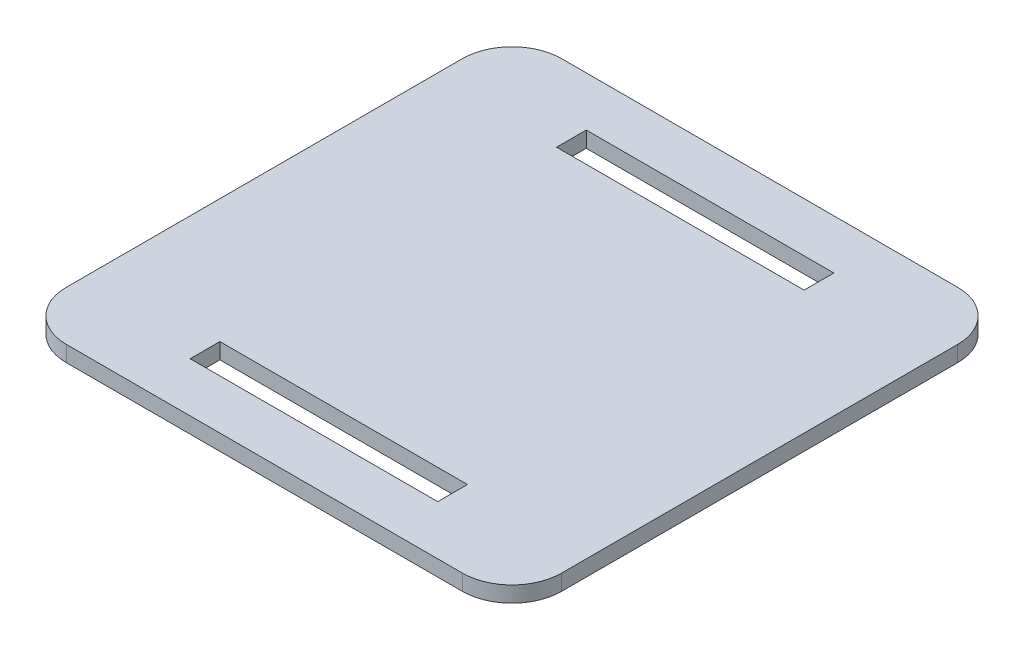
SolidWorks part; units mm, degrees
ref_plane "Front Plane" through (0, 0, 0) normal (0, 0, 1) x (1, 0, 0)
ref_plane "Top Plane" through (0, 0, 0) normal (0, 1, 0) x (1, 0, 0)
ref_plane "Right Plane" through (0, 0, 0) normal (1, 0, 0) x (0, 0, -1)
sketch "Sketch1" plane through (0, 0, 0) normal (0, 1, 0) x (1, 0, 0)
  line L0 (0, 0) -> (0, 50)
  line L1 (0, 0) -> (50, 0)
  line L2 (0, 50) -> (50, 50)
  line L3 (50, 0) -> (50, 50)
  point P0 (0, 0)
extrude "Boss-Extrude1" add sketch "Sketch1" along normal blind 1.6
sketch "Sketch2" plane through (0, 0, 0) normal (0, -1, 0) x (1, 0, 0)
  line L3 (12.5, -5) -> (12.5, -8)
  line L4 (12.5, -5) -> (37.5, -5)
  line L5 (12.5, -8) -> (12.5, -5)
  line L6 (12.5, -8) -> (37.5, -8)
  line L7 (12.5, -5) -> (37.5, -5)
  line L8 (37.5, -8) -> (37.5, -5)
  line L10 (12.5, -45) -> (37.5, -45)
  line L11 (12.5, -45) -> (12.5, -42)
  line L12 (37.5, -45) -> (12.5, -45)
  line L13 (37.5, -45) -> (37.5, -42)
  line L14 (12.5, -45) -> (12.5, -42)
  line L15 (37.5, -42) -> (12.5, -42)
extrude "Cut-Extrude1" cut sketch "Sketch2" against normal blind 1.6 contours L6 L8 L4 L3 | L13 L15 L11 L10
fillet "Fillet1" radius 5 2 edges at (50, 0.8, 0) (0, 0.8, 0)
fillet "Fillet2" radius 5 1 edges at (50, 0.8, -50)
fillet "Fillet3" radius 5 1 edges at (0, 0.8, -50)
